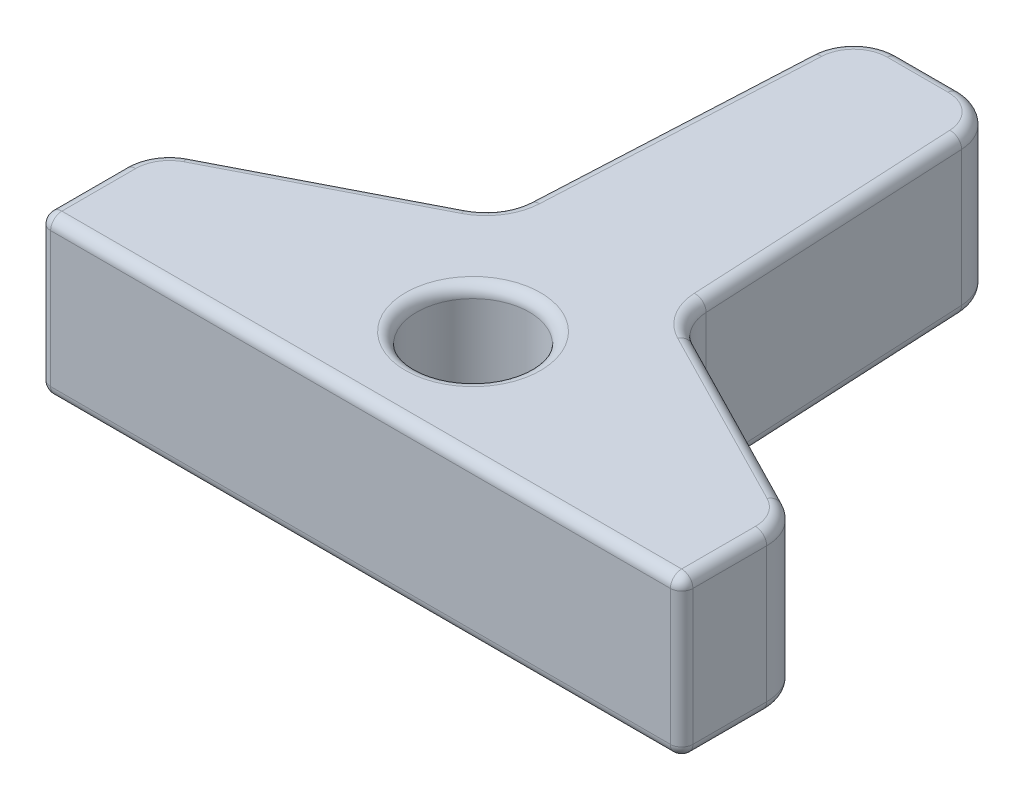
SolidWorks part; units mm, degrees
ref_plane "Front" through (0, 0, 0) normal (0, 0, 1) x (1, 0, 0)
ref_plane "Top" through (0, 0, 0) normal (0, 1, 0) x (1, 0, 0)
ref_plane "Right" through (0, 0, 0) normal (1, 0, 0) x (0, 0, -1)
sketch "Sketch1" plane through (0, 0, 0) normal (0, 1, 0) x (1, 0, 0)
  line L0 (-23.7919, 12.9667) -> (-17.2919, 12.9667)
  line L1 (-17.2919, 12.9667) -> (-16.5419, -2.0333)
  line L2 (-16.5419, -2.0333) -> (-6.2719, -7.2972)
  line L3 (-6.2719, -7.2972) -> (-6.2719, -12.2972)
  line L4 (-6.2719, -12.2972) -> (-34.8118, -12.2972)
  line L5 (-34.8118, -12.2972) -> (-34.8118, -7.2972)
  line L6 (-34.8118, -7.2972) -> (-24.5419, -2.0333)
  line L7 (-24.5419, -2.0333) -> (-23.7919, 12.9667)
  line L8 (-16.5419, -2.0333) -> (-24.5419, -2.0333)
  line L9 (-20.5419, -2.0333) -> (-20.5419, 12.9667)
  circle A0 centre (-20.5419, -7.2972) radius 2.5
  point P9 (-20.5419, 12.9667)
  dimension "D6" = 5
  dimension "D1" = 6.5
  dimension "D2" = 15
  dimension "D3" = 8
  dimension "D4" = 120
  dimension "D5" = 5
  dimension "D7" = 5
extrude "Boss-Extrude1" add sketch "Sketch1" along normal blind 7 contours L9 L8 L1 L0 | L8 L9 L0 L7 | L2 L8 L6 L5 L4 L3
fillet "Fillet1" radius 2 6 edges at (-6.2719, 3.5, 7.2972) (-34.8118, 3.5, 7.2972) (-16.5419, 3.5, 2.0333) (-24.5419, 3.5, 2.0333) (-23.7919, 3.5, -12.9667) (-17.2919, 3.5, -12.9667)
fillet "Fillet2" radius 0.5 32 edges at (-34.8118, 0, 10.4084) (-34.5184, 0, 7.4766) (-29.6468, 0, 4.6499) (-24.8018, 0, 1.8654) (-24.1855, 0, -5.0933) (-23.2678, 0, -12.4158) (-20.5419, 0, -12.9667) (-17.8159, 0, -12.4158) (-6.2719, 0, 10.4084) (-6.5654, 0, 7.4766) (-11.437, 0, 4.6499) (-16.8982, 0, -5.0933) (-16.282, 0, 1.8654) (-16.282, 7, 1.8654) (-6.2719, 7, 10.4084) (-6.5654, 7, 7.4766) (-11.437, 7, 4.6499) (-24.8018, 7, 1.8654) (-29.6468, 7, 4.6499) (-34.5184, 7, 7.4766) (-34.8118, 7, 10.4084) (-16.8982, 7, -5.0933) (-17.8159, 7, -12.4158) (-20.5419, 7, -12.9667) (-23.2678, 7, -12.4158) (-24.1855, 7, -5.0933) (-20.5419, 0, 12.2972) (-20.5419, 7, 12.2972) (-34.8118, 3.5, 12.2972) (-6.2719, 3.5, 12.2972) (-20.5419, 0, 9.7972) (-20.5419, 7, 9.7972)
